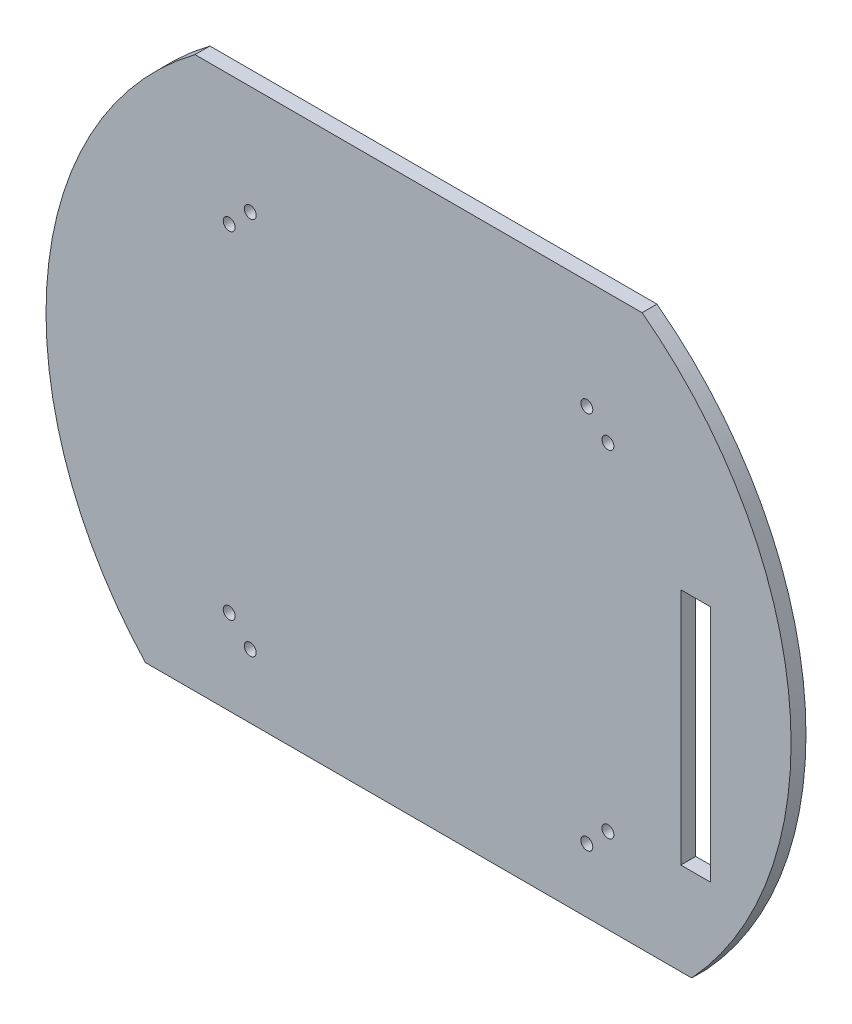
SolidWorks part; units mm, degrees
material "ABS"
ref_plane "Front Plane" through (0, 0, 0) normal (0, 0, 1) x (1, 0, 0)
ref_plane "Top Plane" through (0, 0, 0) normal (0, 1, 0) x (1, 0, 0)
ref_plane "Right Plane" through (0, 0, 0) normal (1, 0, 0) x (0, 0, -1)
sketch "Sketch1" plane through (0, 0, 0) normal (0, 0, 1) x (1, 0, 0)
  circle A0 centre (0, 0) radius 125
  dimension "D1" = 250
extrude "Boss-Extrude1" add sketch "Sketch1" along normal blind 5
sketch "Sketch2" plane through (0, 0, 5) normal (0, 0, 1) x (1, 0, 0)
  line L0 (-63.5355, 56.4645) -> (-56.4645, 63.5355) construction
  line L1 (-60, -60) -> (60, -60) construction
  line L2 (-60, -60) -> (-60, 60) construction
  line L3 (-60, 60) -> (60, 60) construction
  line L4 (60, -60) -> (60, 60) construction
  line L5 (-60, -60) -> (60, 60) construction
  line L6 (-60, 60) -> (60, -60) construction
  line L7 (63.5355, 56.4645) -> (56.4645, 63.5355) construction
  line L8 (63.5355, -56.4645) -> (56.4645, -63.5355) construction
  line L9 (-56.4645, -63.5355) -> (-63.5355, -56.4645) construction
  circle A0 centre (-56.4645, -63.5355) radius 2
  circle A1 centre (-63.5355, -56.4645) radius 2
  circle A2 centre (-56.4645, 63.5355) radius 2
  circle A3 centre (-63.5355, 56.4645) radius 2
  circle A4 centre (56.4645, 63.5355) radius 2
  circle A5 centre (63.5355, 56.4645) radius 2
  circle A6 centre (63.5355, -56.4645) radius 2
  circle A7 centre (56.4645, -63.5355) radius 2
  point P0 (0, 0)
  point P14 (-60, 60)
  point P15 (60, 60)
  point P16 (60, -60)
  point P17 (-60, -60)
  dimension "D8" = 4
  dimension "D9" = 4
  dimension "D10" = 4
  dimension "D11" = 4
  dimension "D12" = 4
  dimension "D13" = 4
  dimension "D14" = 4
  dimension "D15" = 4
  dimension "D2" = 120
  dimension "D3" = 120
  dimension "D4" = 10
  dimension "D5" = 10
  dimension "D6" = 10
  dimension "D7" = 10
extrude "Cut-Extrude1" cut sketch "Sketch2" against normal up to next
sketch "Sketch3" plane through (0, 0, 5) normal (0, 0, 1) x (1, 0, 0)
  line L0 (-91.6515, -85) -> (91.6515, -85)
  arc A0 (-91.6515, -85) -> (91.6515, -85) centre (0, 0) ccw
  circle A1 centre (0, 0) radius 125 construction
  dimension "D1" = 85
extrude "Cut-Extrude2" cut sketch "Sketch3" against normal up to next
sketch "Sketch4" plane through (0, 0, 5) normal (0, 0, 1) x (1, 0, 0)
  line L1 (88, -54) -> (98, -54)
  line L2 (88, -54) -> (88, 26)
  line L3 (88, 26) -> (98, 26)
  line L4 (98, -54) -> (98, 26)
  dimension "D1" = 80
  dimension "D2" = 10
  dimension "D3" = 88
  dimension "D4" = 26
extrude "Cut-Extrude3" cut sketch "Sketch4" against normal up to next
sketch "Sketch5" plane through (0, 0, 5) normal (0, 0, 1) x (1, 0, 0)
  line L0 (-75, 100) -> (75, 100)
  circle A0 centre (0, 0) radius 125
  arc A1 (91.6515, -85) -> (-91.6515, -85) centre (0, 0) ccw construction
  arc M8 (91.6515, -85) -> (-91.6515, -85) centre (0, 0) ccw
  dimension "D1" = 100
extrude "Cut-Extrude4" cut sketch "Sketch5" against normal up to next contours L0 M8
